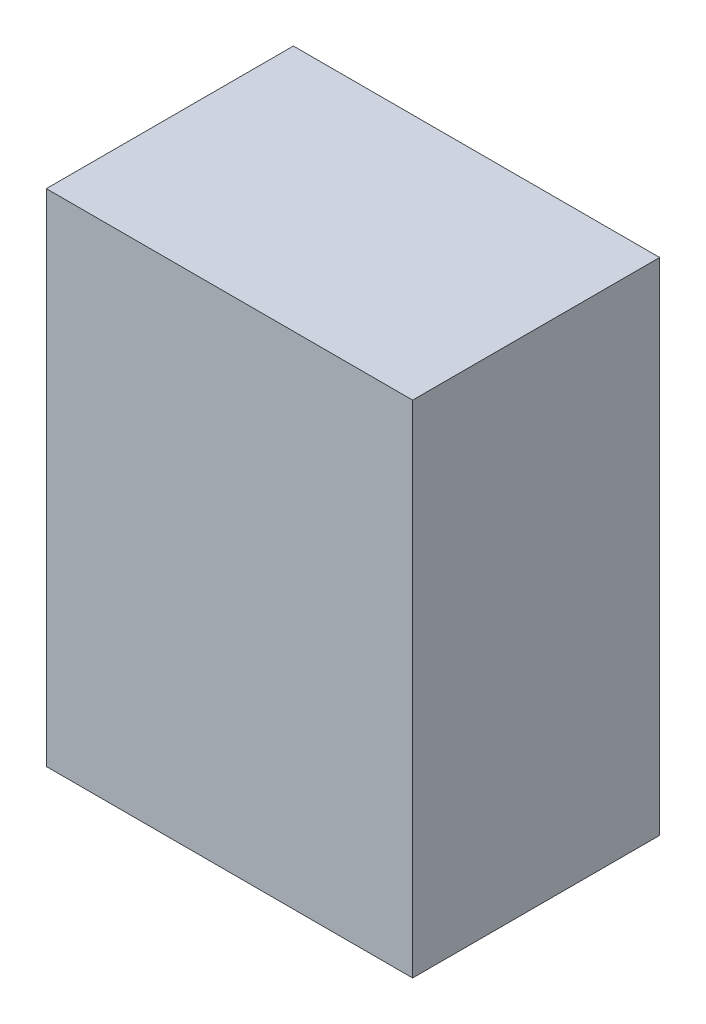
SolidWorks part; units mm, degrees
material "TMAD Battery"
ref_plane "Front Plane" through (0, 0, 0) normal (0, 0, 1) x (1, 0, 0)
ref_plane "Top Plane" through (0, 0, 0) normal (0, 1, 0) x (1, 0, 0)
ref_plane "Right Plane" through (0, 0, 0) normal (1, 0, 0) x (0, 0, -1)
sketch "Sketch1" plane through (0, 0, 0) normal (0, 1, 0) x (1, 0, 0)
  line L1 (86, -58) -> (-86, -58)
  line L2 (86, -58) -> (86, 58)
  line L3 (86, 58) -> (-86, 58)
  line L4 (-86, -58) -> (-86, 58)
  line L5 (86, -58) -> (-86, 58) construction
  line L6 (86, 58) -> (-86, -58) construction
  point P0 (0, 0)
  dimension "D1" = 172
  dimension "D2" = 116
extrude "Boss-Extrude1" add sketch "Sketch1" along normal blind 235
